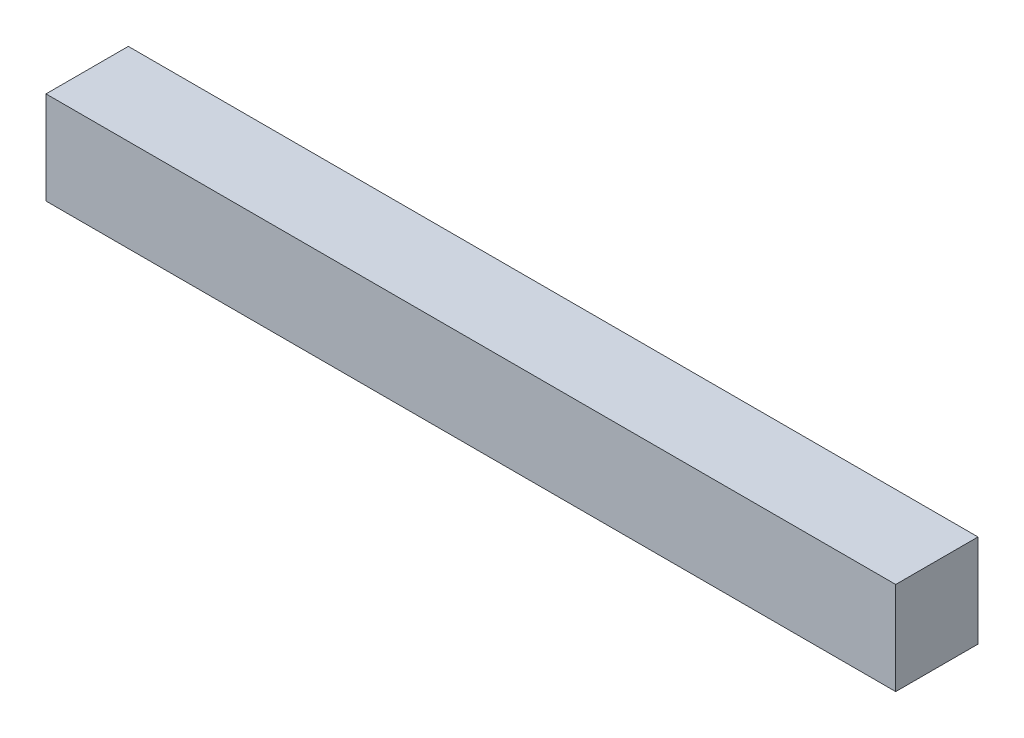
SolidWorks part; units mm, degrees
ref_plane "Front Plane" through (0, 0, 0) normal (0, 0, 1) x (1, 0, 0)
ref_plane "Top Plane" through (0, 0, 0) normal (0, 1, 0) x (1, 0, 0)
ref_plane "Right Plane" through (0, 0, 0) normal (1, 0, 0) x (0, 0, -1)
sketch "Sketch1" plane through (0, 0, 0) normal (0, 0, 1) x (1, 0, 0)
  line L1 (-11763.1951, 4974.9391) -> (-12795.6708, 4974.9391)
  line L2 (-11763.1951, 4974.9391) -> (-11763.1951, 4862.1521)
  line L3 (-11763.1951, 4862.1521) -> (-12795.6708, 4862.1521)
  line L4 (-12795.6708, 4974.9391) -> (-12795.6708, 4862.1521)
extrude "Extrude1" add sketch "Sketch1" along normal blind 100
